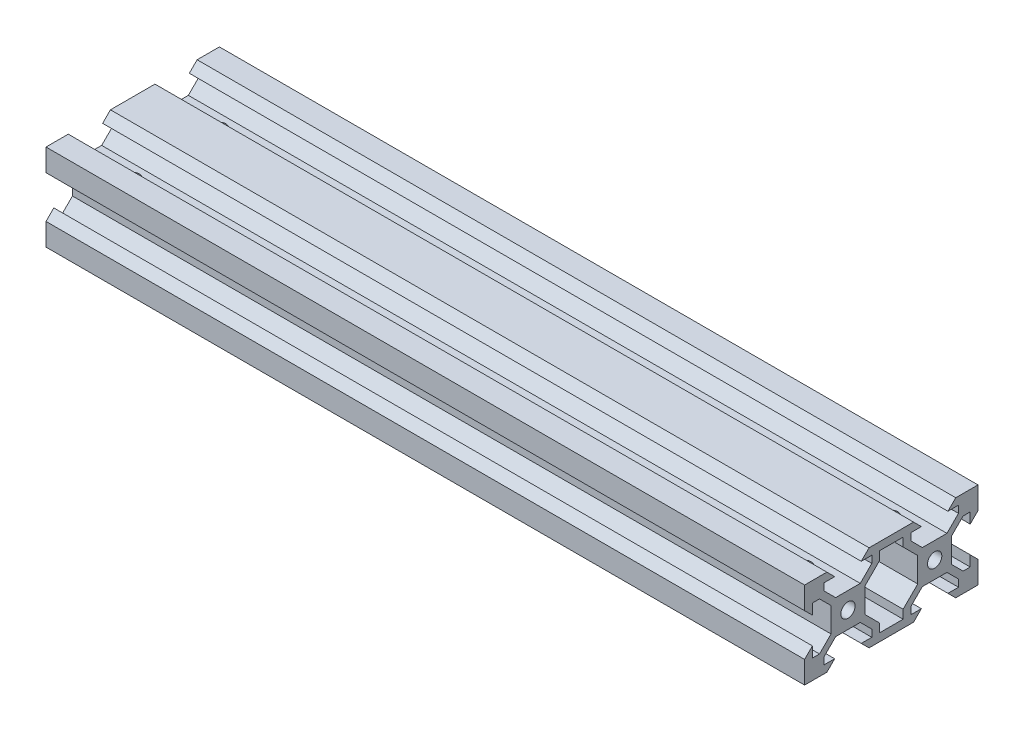
SolidWorks part; units mm, degrees
ref_plane "Front Plane" through (0, 0, 0) normal (0, 0, 1) x (1, 0, 0)
ref_plane "Top Plane" through (0, 0, 0) normal (0, 1, 0) x (1, 0, 0)
ref_plane "Right Plane" through (0, 0, 0) normal (1, 0, 0) x (0, 0, -1)
sketch "Sketch1" plane through (0, 0, 0) normal (0, 1, 0) x (1, 0, 0)
  line L1 (-87.5, -20) -> (87.5, -20)
  line L2 (-87.5, -20) -> (-87.5, 20)
  line L3 (-87.5, 20) -> (87.5, 20)
  line L4 (87.5, -20) -> (87.5, 20)
  line L5 (0, 20) -> (0, -20) construction
  line L6 (-87.5, 0) -> (87.5, 0) construction
  point P0 (0, 0)
  dimension "D1" = 175
  dimension "D2" = 40
extrude "Boss-Extrude1" add sketch "Sketch1" along normal blind 20
sketch "Sketch7" plane through (87.5, 0, 0) normal (1, 0, 0) x (0, 0, -1)
  line L0 (-20, 0) -> (20, 0) construction
  line L1 (-20, 20) -> (20, 20) construction
  line L2 (-20, 20) -> (-20, 0) construction
  line L3 (-20, 0) -> (20, 0) construction
  line L4 (0, 20) -> (0, 0) construction
  line L5 (-7.1593, 13.9) -> (-4.4993, 16.56)
  line L12 (-12.8393, 13.9) -> (-7.1593, 13.9)
  line L14 (-12.8393, 13.9) -> (-15.4993, 16.56)
  line L15 (-4.4993, 16.56) -> (-4.4993, 18.2)
  line L20 (-15.4993, 16.56) -> (-15.4993, 18.2)
  line L21 (-4.4993, 18.2) -> (-6.9343, 18.2)
  line L22 (-13.0643, 18.2) -> (-14.8643, 20)
  line L23 (-15.4993, 18.2) -> (-13.0643, 18.2)
  line L24 (-18.2, 13.0643) -> (-20, 14.8643)
  line L25 (-20, 20) -> (-20, 14.8643)
  line L26 (-6.9343, 18.2) -> (-5.1343, 20)
  line L27 (-18.2, 13.0643) -> (-18.2, 15.4993)
  line L28 (-18.2, 15.4993) -> (-16.56, 15.4993)
  line L29 (-16.56, 15.4993) -> (-13.9, 12.8393)
  line L30 (-14.8643, 20) -> (-20, 20)
  line L31 (-13.9, 12.8393) -> (-13.9, 7.1593)
  line L36 (-6.0987, 12.8393) -> (-6.0987, 7.1593)
  line L37 (-4.4993, 16.56) -> (-7.1593, 13.9) [skipped]
  line L38 (-6.0987, 12.8393) -> (-3.4387, 15.4993) [skipped]
  line L39 (-3.4387, 15.4993) -> (-1.7987, 15.4993) [skipped]
  line L40 (-1.7987, 15.4993) -> (-1.7987, 13.0643) [skipped]
  line L41 (-1.7987, 13.0643) -> (0.0013, 14.8643) [skipped]
  line L42 (0.0013, 14.8643) -> (0.0013, 20) [skipped]
  line L43 (0.0013, 20) -> (-5.1343, 20) [skipped]
  line L44 (-6.9343, 18.2) -> (-5.1343, 20) [skipped]
  line L45 (-6.9343, 18.2) -> (-4.4993, 18.2) [skipped]
  line L46 (-4.4993, 18.2) -> (-4.4993, 16.56) [skipped]
  line L48 (-6.0987, 7.1593) -> (-2.73, 3.7907)
  line L49 (-7.1593, 6.0987) -> (-4.4993, 3.4387)
  line L50 (-4.4993, 3.4387) -> (-4.4993, 1.7987)
  line L51 (-4.4993, 1.7987) -> (-6.9343, 1.7987)
  line L52 (-6.9343, 1.7987) -> (-5.1343, -0.0013)
  line L54 (-5.1343, 20) -> (5.1343, 20)
  line L58 (-2.73, 18.2) -> (2.73, 18.2)
  line L59 (-15.4993, 3.4387) -> (-12.8393, 6.0987)
  line L60 (-13.9, 7.1593) -> (-16.56, 4.4993)
  line L61 (-16.56, 4.4993) -> (-18.2, 4.4993)
  line L62 (-18.2, 4.4993) -> (-18.2, 6.9343)
  line L63 (-18.2, 6.9343) -> (-20, 5.1343)
  line L64 (-20, 5.1343) -> (-20, -0.0013)
  line L65 (-20, -0.0013) -> (-14.8643, -0.0013)
  line L66 (-13.0643, 1.7987) -> (-14.8643, -0.0013)
  line L67 (-13.0643, 1.7987) -> (-15.4993, 1.7987)
  line L68 (-15.4993, 1.7987) -> (-15.4993, 3.4387)
  line L69 (-6.0987, 12.8393) -> (-2.73, 16.208)
  line L70 (-12.8393, 6.0987) -> (-7.1593, 6.0987)
  line L71 (-3.4387, 4.4993) -> (-6.0987, 7.1593) [skipped]
  line L72 (-1.7987, 4.4993) -> (-3.4387, 4.4993) [skipped]
  line L73 (-1.7987, 6.9343) -> (0.0013, 5.1343) [skipped]
  line L74 (-1.7987, 6.9343) -> (-1.7987, 4.4993) [skipped]
  line L87 (-2.73, 16.208) -> (-2.73, 18.2)
  line L88 (-2.73, 3.7907) -> (-2.73, 1.7987)
  line L113 (0.0013, -0.0013) -> (0.0013, 5.1343) [skipped]
  line L114 (-5.1343, -0.0013) -> (0.0013, -0.0013) [skipped]
  line L115 (-2.73, 1.7987) -> (2.73, 1.7987)
  line L116 (-5.1343, -0.0013) -> (0, 0)
  line L117 (20, 20) -> (20, 0) construction
  line L118 (5.1343, -0.0013) -> (0, 0)
  line L119 (2.73, 3.7907) -> (2.73, 1.7987)
  line L120 (2.73, 16.208) -> (2.73, 18.2)
  line L121 (12.8393, 6.0987) -> (7.1593, 6.0987)
  line L122 (6.0987, 12.8393) -> (2.73, 16.208)
  line L123 (15.4993, 1.7987) -> (15.4993, 3.4387)
  line L124 (13.0643, 1.7987) -> (15.4993, 1.7987)
  line L125 (13.0643, 1.7987) -> (14.8643, -0.0013)
  line L126 (20, -0.0013) -> (14.8643, -0.0013)
  line L127 (20, 5.1343) -> (20, -0.0013)
  line L128 (18.2, 6.9343) -> (20, 5.1343)
  line L129 (18.2, 4.4993) -> (18.2, 6.9343)
  line L130 (16.56, 4.4993) -> (18.2, 4.4993)
  line L131 (13.9, 7.1593) -> (16.56, 4.4993)
  line L132 (15.4993, 3.4387) -> (12.8393, 6.0987)
  line L133 (6.9343, 1.7987) -> (5.1343, -0.0013)
  line L134 (4.4993, 1.7987) -> (6.9343, 1.7987)
  line L135 (4.4993, 3.4387) -> (4.4993, 1.7987)
  line L136 (7.1593, 6.0987) -> (4.4993, 3.4387)
  line L137 (6.0987, 7.1593) -> (2.73, 3.7907)
  line L138 (6.0987, 12.8393) -> (6.0987, 7.1593)
  line L139 (13.9, 12.8393) -> (13.9, 7.1593)
  line L140 (14.8643, 20) -> (20, 20)
  line L141 (16.56, 15.4993) -> (13.9, 12.8393)
  line L142 (18.2, 15.4993) -> (16.56, 15.4993)
  line L143 (18.2, 13.0643) -> (18.2, 15.4993)
  line L144 (6.9343, 18.2) -> (5.1343, 20)
  line L145 (20, 20) -> (20, 14.8643)
  line L146 (18.2, 13.0643) -> (20, 14.8643)
  line L147 (15.4993, 18.2) -> (13.0643, 18.2)
  line L148 (13.0643, 18.2) -> (14.8643, 20)
  line L149 (4.4993, 18.2) -> (6.9343, 18.2)
  line L150 (15.4993, 16.56) -> (15.4993, 18.2)
  line L151 (4.4993, 16.56) -> (4.4993, 18.2)
  line L152 (12.8393, 13.9) -> (15.4993, 16.56)
  line L153 (12.8393, 13.9) -> (7.1593, 13.9)
  line L154 (7.1593, 13.9) -> (4.4993, 16.56)
  circle A0 centre (-10, 10) radius 1.65
  circle A1 centre (10, 10) radius 1.65
  point P36 (0, 1.7987)
  point P81 (-9.9993, 9.9993)
  point P84 (0, 18.2)
  point P103 (9.9993, 9.9993)
  line M26 (-20, 0) -> (20, 0)
  line M27 (20, 0) -> (20, 20)
  line M28 (20, 20) -> (-20, 20)
  line M29 (-20, 20) -> (-20, 0)
  dimension "D1" = 4.3
  dimension "D11" = 3.3
  dimension "D2" = 6.13
  dimension "D3" = 11
  dimension "D4" = 4.3
  dimension "D5" = 4.3
  dimension "D6" = 1.8
  dimension "D7" = 1.8
  dimension "D8" = 1.5
  dimension "D9" = 1.5
  dimension "D12" = 1.5
  dimension "D13" = 5.68
  dimension "D10" = 4
extrude "Cut-Extrude13" cut sketch "Sketch7" against normal through all contours L21 L26 L22 L23 L20 L14 L12 L5 L15 M28 | L63 L62 L61 L60 L31 L29 L28 L27 L24 M29 | L70 L59 L68 L67 L66 L52 L51 L50 L49 M26 | L138 L122 L120 L58 L87 L69 L36 L48 L88 L115 L119 L137 | L121 L136 L135 L134 L133 L125 L124 L123 L132 M26 | L146 L143 L142 L141 L139 L131 L130 L129 L128 M27 | L154 L153 L152 L150 L147 L148 L144 L149 L151 M28 | A0 | A1
sketch "Sketch17" plane through (-87.5, 0, 0) normal (-1, 0, 0) x (0, 0, 1)
  circle A0 centre (-10, 10) radius 1.55
  circle A1 centre (10, 10) radius 1.55
  circle A2 centre (-10, 10) radius 1.65
  circle A3 centre (10, 10) radius 1.65
  dimension "D1" = 3.1
extrude "Boss-Extrude2" add sketch "Sketch17" against normal blind 15
sketch "Sketch16" plane through (0, 13.9, 0) normal (0, 1, 0) x (1, 0, 0)
  line L4 (87.5, 12.8393) -> (87.5, 7.1593) construction
  line L5 (87.5, -12.8393) -> (87.5, -7.1593) construction
  circle A0 centre (77.5, -9.9993) radius 1.5
  circle A1 centre (77.5, 9.9993) radius 1.5
  dimension "D2" = 3
  dimension "D3" = 10
  dimension "D4" = 10
extrude "Cut-Extrude11" cut sketch "Sketch16" against normal through all
ref_plane "Plane1" through (0, 0, 0) normal (-1, 0, 0) x (0, 0, 1)
mirror "Mirror1" about plane through (0, 0, 0) normal (-1, 0, 0) of "Cut-Extrude11"
